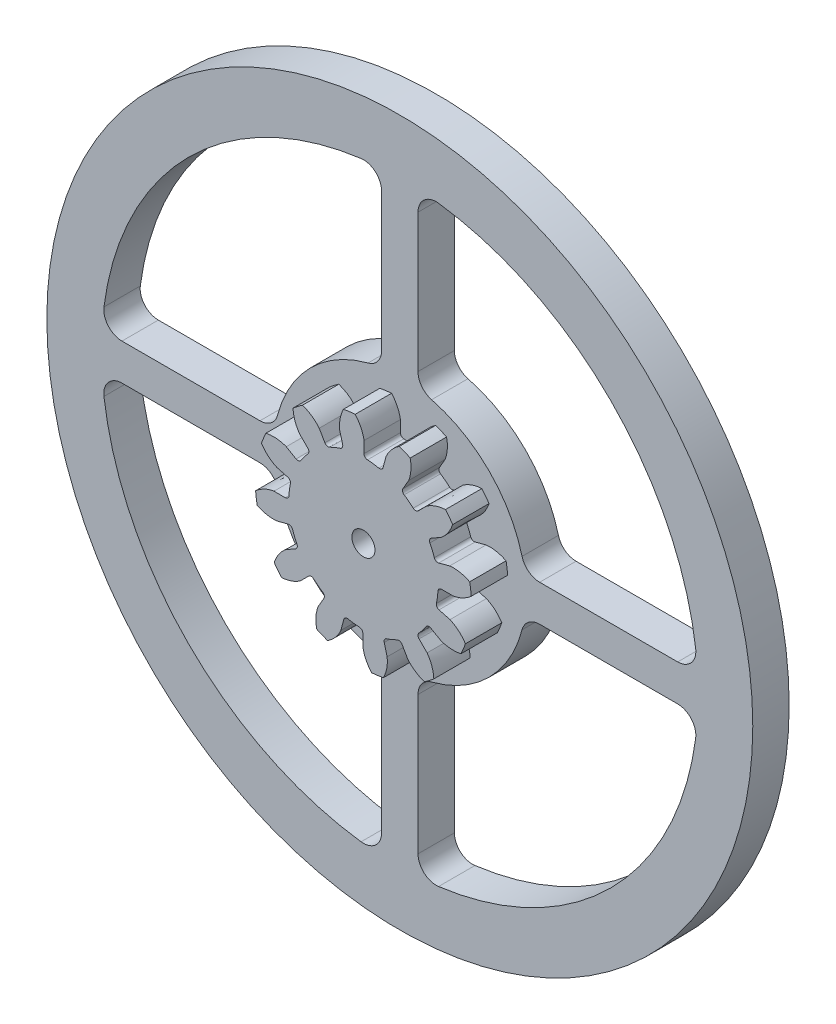
SolidWorks part; units mm, degrees
ref_plane "Front" through (0, 0, 0) normal (0, 0, 1) x (1, 0, 0)
ref_plane "Top" through (0, 0, 0) normal (0, 1, 0) x (1, 0, 0)
ref_plane "Right" through (0, 0, 0) normal (1, 0, 0) x (0, 0, -1)
sketch "Sketch1" plane through (0, 0, 0) normal (0, 0, 1) x (1, 0, 0)
  line L0 (-152.4, 0) -> (152.4, 0) construction
  circle A0 centre (0, 0) radius 14.859
  circle A1 centre (0, 0) radius 12.7 construction
  circle A3 centre (0, 0) radius 10.251 construction
  dimension "D1" = 2.449
  dimension "D2" = 4.608
  dimension "D3" = 2.159
extrude "Boss-Extrude1" add sketch "Sketch1" against normal blind 5
sketch "Sketch3" plane through (0, 0, 0) normal (0, 0, 1) x (1, 0, 0)
  line L0 (0, 0) -> (0, 14.859) construction
  line L1 (-3.0785, 11.9038) -> (0, 12.7)
  line L2 (-9.5921, 12.7) -> (9.5921, 12.7) construction
  line L3 (-9.2865, 10.2983) -> (9.2865, 15.1017) construction
  line L4 (-3.0785, 11.9038) -> (0, 0) construction
  line L5 (-7.8523, 9.4615) -> (0, 0) construction
  line L6 (-7.8523, 9.4615) -> (-1.2457, 14.9445) construction
  line L7 (-2.1466, 12.1066) -> (0, 0) construction
  line L8 (-2.1466, 12.1066) -> (0.045, 12.4952) construction
  arc A0 (-3.0785, 11.9038) -> (-7.8523, 9.4615) centre (0, 0) ccw
  circle A1 centre (0, 0) radius 12.7 construction
  circle A2 centre (0, 0) radius 12.2955 construction
  arc A3 (-3.0785, 11.9038) -> (-2.1466, 12.1066) centre (0, 0) cw
  circle A4 centre (0, 0) radius 14.859 construction
  point P6 (0, 12.7)
  dimension "D1" = 3.1798
  dimension "Pressure Angle" = 14.5
  dimension "D2" = 5.4057
  dimension "D3" = 8.5855
  dimension "D4" = 0.9539
  dimension "D5" = 2.2259
sketch "Sketch4" plane through (0, 0, 0) normal (0, 0, 1) x (1, 0, 0)
  line L0 (0, 0) -> (1.6435, 12.4836) construction
  line L1 (0.0801, 12.2952) -> (0.0801, 10.2507)
  line L2 (0, 12.7) -> (3.287, 12.2673) construction
  line L3 (3.1048, 11.897) -> (2.5757, 9.9222)
  line L4 (0.0801, 10.2507) -> (0, 0) construction
  line L5 (0, 0) -> (0, 14.859) construction
  line L6 (-7.8523, 9.4615) -> (-1.2457, 14.9445) construction
  line L7 (-7.8523, 9.4615) -> (-1.2457, 14.9445) construction
  arc A0 (2.5757, 9.9222) -> (0.0801, 10.2507) centre (0, 0) ccw
  arc A1 (0, 12.7) -> (3.287, 12.2673) centre (0, 0) cw construction
  circle A2 centre (0, 0) radius 12.7 construction
  circle A3 centre (0, 0) radius 12.2955 construction
  circle A4 centre (0, 0) radius 10.251 construction
  arc A5 (5.0712, 14.1129) -> (-1.2457, 14.9445) centre (0, 0) ccw
  spline S0 degree 2 poles (-1.2457, 14.9445) (-0.1467, 13.7689) (0.0801, 12.2952) knots 0 0 0 1 1 1
  spline S1 degree 2 poles (5.0712, 14.1129) (3.7054, 13.2617) (3.1048, 11.897) knots 0 0 0 1 1 1
  dimension "D1" = 3.3249
extrude "Cut-Extrude1" cut sketch "Sketch4" against normal through all
fillet "Fillet1" radius 0.4987 2 edges at (2.5757, 9.9222, -2.5) (0.0801, 10.2507, -2.5)
pattern_circular "CirPattern1" count 12 over 360 about axis through (0, 0, -5) along (0, 0, 1) of "Cut-Extrude1", "Fillet1"
sketch "Sketch5" plane through (0, 0, 0) normal (0, 0, 1) x (1, 0, 0)
  circle A0 centre (0, 0) radius 1.5875
  circle A1 centre (0, 0) radius 6.35 construction
  dimension "Bore Min" = 3.175
  dimension "Bore Max" = 12.7
extrude "Cut-Extrude2" cut sketch "Sketch5" against normal through all
sketch "Pitch Dia" plane through (0, 0, 0) normal (0, 0, 1) x (1, 0, 0)
  circle A0 centre (0, 0) radius 12.7 construction
  circle A1 centre (0, 0) radius 12.7
sketch "Sketch6" plane through (0, 0, -5) normal (0, 0, -1) x (-1, 0, 0)
  circle A0 centre (0, 0) radius 48.5103
  circle A1 centre (0, 0) radius 1.5875
  dimension "D1" = 97.0206
extrude "Boss-Extrude2" add sketch "Sketch6" along normal blind 5 contours A0
sketch "Sketch7" plane through (0, 0, -5) normal (0, 0, 1) x (1, 0, 0)
  line L8 (0, 14.859) -> (0, 43.5103) construction
  line L9 (14.859, 0) -> (43.5103, 0) construction
  line L10 (2.5, 19.2193) -> (2.5, 38.1843)
  line L11 (19.2193, 2.5) -> (38.1843, 2.5)
  line L12 (17.178, 2.5) -> (40.934, 2.5) construction
  line L13 (2.5, 17.178) -> (2.5, 40.934) construction
  line L18 (19.2193, -2.5) -> (38.1843, -2.5)
  line L19 (2.5, -19.2193) -> (2.5, -38.1843)
  line L22 (14.859, 0) -> (43.5103, 0) construction
  line L23 (0, -14.859) -> (0, -43.5103) construction
  line L32 (-2.5, -19.2193) -> (-2.5, -38.1843)
  line L33 (-19.2193, -2.5) -> (-38.1843, -2.5)
  line L36 (0, -14.859) -> (0, -43.5103) construction
  line L37 (-14.859, 0) -> (-43.5103, 0) construction
  line L40 (-19.2193, 2.5) -> (-38.1843, 2.5)
  line L41 (-2.5, 19.2193) -> (-2.5, 38.1843)
  line L44 (-14.859, 0) -> (-43.5103, 0) construction
  line L45 (0, 14.859) -> (0, 43.5103) construction
  line L56 (0, 0) -> (0, -14.859) [skipped]
  line L57 (0, 0) -> (-14.859, 0) [skipped]
  arc A33 (14.859, 0) -> (0, 14.859) centre (0, 0) ccw construction
  arc A36 (43.5103, 0) -> (0, 43.5103) centre (0, 0) ccw construction
  circle A45 centre (0, 0) radius 48.5103 construction
  arc A46 (40.6632, 5.3246) -> (5.3246, 40.6632) centre (0, 0) ccw
  arc A53 (16.7998, 4.3706) -> (4.3706, 16.7998) centre (0, 0) ccw
  arc A54 (40.934, 2.5) -> (2.5, 40.934) centre (0, 0) ccw construction
  arc A61 (40.6632, 5.3246) -> (38.1843, 2.5) centre (38.1843, 5) cw
  arc A62 (17.178, 2.5) -> (2.5, 17.178) centre (0, 0) ccw construction
  arc A69 (19.2193, 2.5) -> (16.7998, 4.3706) centre (19.2193, 5) cw
  arc A70 (2.5, 19.2193) -> (4.3706, 16.7998) centre (5, 19.2193) ccw
  arc A77 (2.5, 38.1843) -> (5.3246, 40.6632) centre (5, 38.1843) cw
  arc A78 (5.3246, -40.6632) -> (40.6632, -5.3246) centre (0, 0) ccw
  arc A85 (4.3706, -16.7998) -> (16.7998, -4.3706) centre (0, 0) ccw
  arc A86 (5.3246, -40.6632) -> (2.5, -38.1843) centre (5, -38.1843) cw
  arc A93 (2.5, -19.2193) -> (4.3706, -16.7998) centre (5, -19.2193) cw
  arc A94 (19.2193, -2.5) -> (16.7998, -4.3706) centre (19.2193, -5) ccw
  arc A96 (38.1843, -2.5) -> (40.6632, -5.3246) centre (38.1843, -5) cw
  arc A97 (0, -14.859) -> (14.859, 0) centre (0, 0) ccw construction
  arc A98 (0, -43.5103) -> (43.5103, 0) centre (0, 0) ccw construction
  arc A99 (-40.6632, -5.3246) -> (-5.3246, -40.6632) centre (0, 0) ccw
  arc A100 (-16.7998, -4.3706) -> (-4.3706, -16.7998) centre (0, 0) ccw
  arc A101 (-40.6632, -5.3246) -> (-38.1843, -2.5) centre (-38.1843, -5) cw
  arc A102 (-19.2193, -2.5) -> (-16.7998, -4.3706) centre (-19.2193, -5) cw
  arc A103 (-2.5, -19.2193) -> (-4.3706, -16.7998) centre (-5, -19.2193) ccw
  arc A104 (-2.5, -38.1843) -> (-5.3246, -40.6632) centre (-5, -38.1843) cw
  arc A105 (-14.859, 0) -> (0, -14.859) centre (0, 0) ccw construction
  arc A106 (-43.5103, 0) -> (0, -43.5103) centre (0, 0) ccw construction
  arc A107 (-5.3246, 40.6632) -> (-40.6632, 5.3246) centre (0, 0) ccw
  arc A108 (-4.3706, 16.7998) -> (-16.7998, 4.3706) centre (0, 0) ccw
  arc A109 (-5.3246, 40.6632) -> (-2.5, 38.1843) centre (-5, 38.1843) cw
  arc A110 (-2.5, 19.2193) -> (-4.3706, 16.7998) centre (-5, 19.2193) cw
  arc A111 (-19.2193, 2.5) -> (-16.7998, 4.3706) centre (-19.2193, 5) ccw
  arc A112 (-38.1843, 2.5) -> (-40.6632, 5.3246) centre (-38.1843, 5) cw
  arc A113 (0, 14.859) -> (-14.859, 0) centre (0, 0) ccw construction
  arc A114 (0, 43.5103) -> (-43.5103, 0) centre (0, 0) ccw construction
  point P0 (0, 0)
  point P15 (0, 0)
  point P18 (0, 0)
  point P23 (0, 0)
  point P26 (0, 0)
  point P29 (0, 0)
  point P32 (0, 0)
  point P41 (0, 0)
  point P58 (0, 0)
  point P86 (0, 0)
  point P99 (0, 0)
  dimension "D1" = 5
  dimension "D2" = 2.5
  dimension "D3" = 2.5
extrude "Cut-Extrude3" cut sketch "Sketch7" against normal through all
equation "\"D1@Sketch4\" = 1.5708/(\"Number of Teeth@Sketch1\"/\"Ptich Dia@Sketch1\")"
equation "\"D1@CirPattern1\" = \"Number of Teeth@Sketch1\""
equation "\"D1@Fillet1\" = \"D1@Sketch4\"*.15"
equation "\"D1@Sketch1\" = 1.157/(\"Number of Teeth@Sketch1\"/\"Ptich Dia@Sketch1\")"
